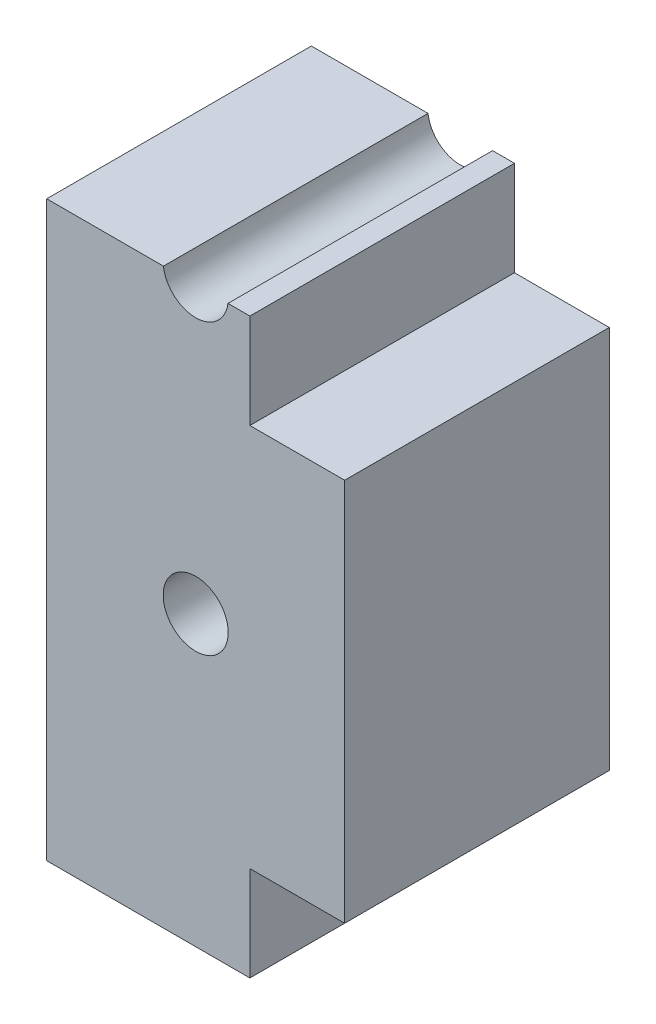
SolidWorks part; units mm, degrees
ref_plane "Front Plane" through (0, 0, 0) normal (0, 0, 1) x (1, 0, 0)
ref_plane "Top Plane" through (0, 0, 0) normal (0, 1, 0) x (1, 0, 0)
ref_plane "Right Plane" through (0, 0, 0) normal (1, 0, 0) x (0, 0, -1)
sketch "Sketch2" plane through (0, 0, 0) normal (0, 0, 1) x (1, 0, 0)
  line L0 (8.25, -152.4) -> (8.25, 152.4) construction
  line L1 (8.25, -39.1052) -> (-8.25, -39.1052)
  line L2 (8.25, -39.1052) -> (8.25, -7.3552)
  line L3 (8.25, -7.3552) -> (-8.25, -7.3552)
  line L4 (-8.25, -39.1052) -> (-8.25, -7.3552)
  line L5 (-8.25, -152.4) -> (-8.25, 152.4) construction
extrude "Boss-Extrude1" add sketch "Sketch2" along normal up to surface (14.655 mm away)
sketch "Sketch3" plane through (0, 0, 14.655) normal (0, 0, 1) x (1, 0, 0)
  line L0 (3.6, -23.1367) -> (3.6, -7.1367) construction
  line L1 (3.6, -26.7367) -> (-3.6, -26.7367)
  line L2 (3.6, -26.7367) -> (3.6, -3.5367)
  line L3 (3.6, -3.5367) -> (-3.6, -3.5367)
  line L4 (-3.6, -26.7367) -> (-3.6, -3.5367)
  line L5 (-4.4, -26.7367) -> (0, -26.7367) construction
  line L6 (0, -3.5367) -> (-4.4, -3.5367) construction
  circle A0 centre (0, -23.1367) radius 2.4 construction
  dimension "D1" = 3.6
extrude "Boss-Extrude2" [suppressed] add sketch "Sketch3" along normal up to surface (6 mm away)
sketch "Sketch4" [suppressed] plane through (0, 0, 11.81) normal (0, 0, 1) x (1, 0, 0)
  circle A4 centre (0, -31.2302) radius 2.8
  circle A5 centre (0, -15.2302) radius 2.8
extrude "Cut-Extrude1" [suppressed] cut sketch "Sketch4" against normal through all
sketch "Sketch5" plane through (0, 0, 14.655) normal (0, 0, 1) x (1, 0, 0)
  line L0 (3, -152.4) -> (3, 152.4) construction
  line L1 (8.25, -39.1052) -> (3, -39.1052)
  line L2 (8.25, -39.1052) -> (8.25, -33.8552)
  line L3 (8.25, -33.8552) -> (3, -33.8552)
  line L4 (3, -39.1052) -> (3, -33.8552)
  line L5 (8.25, -7.3552) -> (3, -7.3552)
  line L6 (8.25, -7.3552) -> (8.25, -12.6052)
  line L7 (8.25, -12.6052) -> (3, -12.6052)
  line L8 (3, -7.3552) -> (3, -12.6052)
extrude "Cut-Extrude2" cut sketch "Sketch5" against normal through all
sketch "Sketch6" plane through (0, 0, 14.655) normal (0, 0, 1) x (1, 0, 0)
  circle A0 centre (0, -7.1367) radius 2.4 construction
  circle A1 centre (0, -23.1367) radius 2.4 construction
  circle A2 centre (0, -7.1367) radius 2.4 construction
  circle A3 centre (0, -23.1367) radius 2.4 construction
  circle A4 centre (0, -23.1367) radius 1.8
  circle A5 centre (0, -7.1367) radius 1.8
  dimension "D1" = 0.6
extrude "Cut-Extrude3" cut sketch "Sketch6" against normal through all
